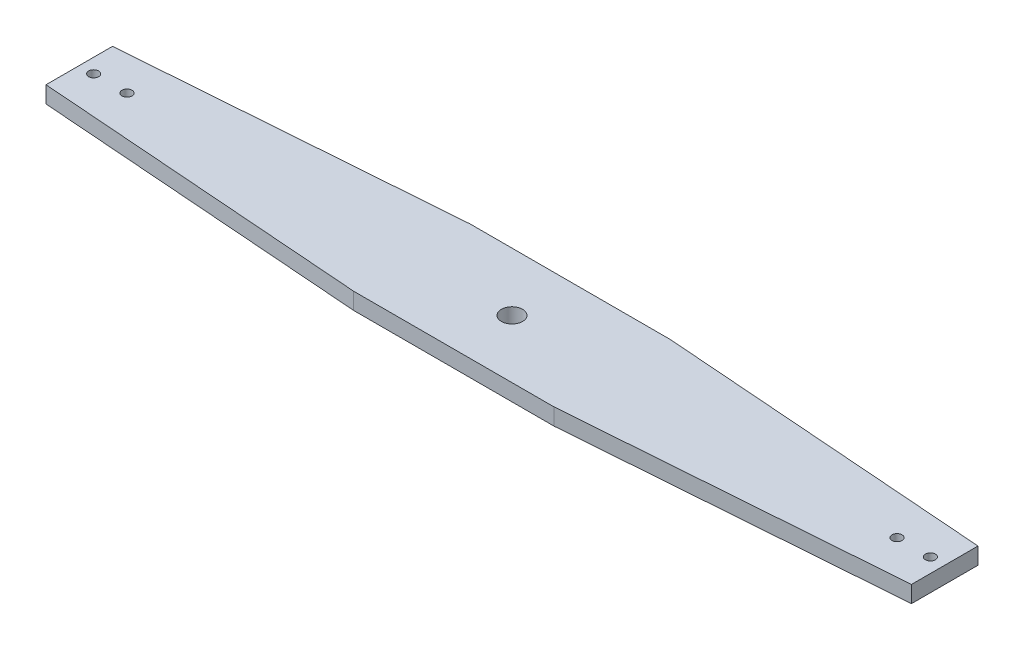
SolidWorks part; units mm, degrees
ref_plane "Front Plane" through (0, 0, 0) normal (0, 0, 1) x (1, 0, 0)
ref_plane "Top Plane" through (0, 0, 0) normal (0, 1, 0) x (1, 0, 0)
ref_plane "Right Plane" through (0, 0, 0) normal (1, 0, 0) x (0, 0, -1)
sketch "Sketch1" plane through (0, 0, 0) normal (0, 1, 0) x (1, 0, 0)
  line L0 (-60, 34.925) -> (60, 34.925)
  line L1 (60, 34.925) -> (259.4381, 19.9438)
  line L2 (-60, 34.925) -> (-259.4381, 19.9438)
  line L3 (-259.4381, -19.9438) -> (-60, -34.925)
  line L4 (-60, -34.925) -> (60, -34.925)
  line L5 (60, -34.925) -> (259.4381, -19.9438)
  line L6 (-259.4381, 19.9438) -> (-259.4381, -19.9438)
  line L7 (-250.825, 0) -> (250.825, 0) construction
  line L8 (0, 34.925) -> (0, -34.925) construction
  line L9 (259.4381, 19.9438) -> (259.4381, -19.9438)
  circle A0 centre (-250.825, 0) radius 3
  circle A1 centre (250.825, 0) radius 3
  circle A4 centre (0, 0) radius 6.35
  circle A5 centre (-230.825, 0) radius 3
  circle A6 centre (230.825, 0) radius 3
  point P15 (0, 0)
  point P16 (0, 0)
  dimension "D2" = 6
  dimension "D3" = 6
  dimension "D13" = 12.7
  dimension "D16" = 6
  dimension "D1" = 501.65
  dimension "D4" = 120
  dimension "D5" = 120
  dimension "D6" = 200
  dimension "D7" = 200
  dimension "D8" = 200
  dimension "D9" = 200
  dimension "D10" = 69.85
  dimension "D14" = 20
  dimension "D15" = 20
  dimension "D17" = 39.8876
  dimension "D11" = 8.592
extrude "Boss-Extrude1" add sketch "Sketch1" along normal blind 10
equation "\"D5@Sketch1\"=\"D4@Sketch1\""
equation "\"D8@Sketch1\"=\"D7@Sketch1\""
equation "\"D9@Sketch1\"=\"D7@Sketch1\""
equation "\"D6@Sketch1\"=\"D7@Sketch1\""
